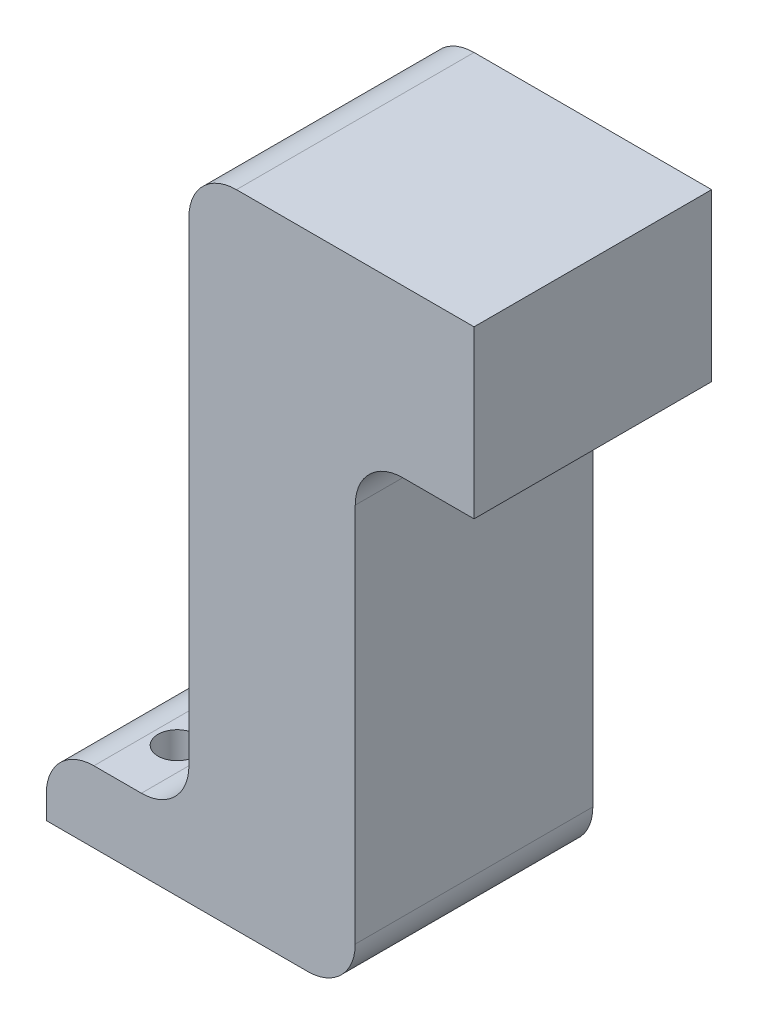
SolidWorks part; units mm, degrees
ref_plane "Front Plane" through (0, 0, 0) normal (0, 0, 1) x (1, 0, 0)
ref_plane "Top Plane" through (0, 0, 0) normal (0, 1, 0) x (1, 0, 0)
ref_plane "Right Plane" through (0, 0, 0) normal (1, 0, 0) x (0, 0, -1)
sketch "Sketch1" plane through (0, 0, 0) normal (0, 0, 1) x (1, 0, 0)
  line L0 (-1.4642, 0.25) -> (-1.4642, -4.75)
  line L5 (-1.4642, 0.25) -> (1.5358, 0.25)
  line L6 (-1.4642, 0.25) -> (-1.4642, 2)
  line L7 (-1.4642, 2) -> (1.5358, 2)
  line L8 (1.5358, 0.25) -> (1.5358, 2)
  line L9 (-1.4642, -4.75) -> (-2.9642, -4.75)
  line L10 (-1.4642, -4.75) -> (-1.4642, -4)
  line L11 (-1.4642, -4) -> (-2.9642, -4)
  line L12 (-2.9642, -4.75) -> (-2.9642, -4)
  line L13 (-1.4642, 0.25) -> (0.2858, 0.25)
  line L14 (-1.4642, -4.75) -> (0.2858, -4.75)
  line L15 (0.2858, 0.25) -> (0.2858, -4.75)
  dimension "D1" = 1.75
  dimension "D2" = 3
  dimension "D3" = 0
  dimension "D4" = 1.75
  dimension "D5" = 0.75
  dimension "D6" = 5
  dimension "D7" = 1.5
extrude "Boss-Extrude1" add sketch "Sketch1" along normal blind 1.875 and the other way blind 0.625 contours L5 L8 L7 L6 | L12 L9 L0 L11
fillet "Fillet1" radius 0.5 5 edges at (0.2858, 0.25, 0.625) (-1.4642, 2, 0.625) (-2.9642, -4, 0.625) (0.2858, -4.75, 0.625) (-1.4642, -4, 0.625)
hole_wizard "Ø0.4 (0.4) Diameter Hole1" positions "Sketch2" profile "Sketch3" hole size "Ø0.4" standard "DIN" end condition through all
sketch "Sketch2" plane through (0, -4, 0) normal (0, 1, 0) x (1, 0, 0)
  line L0 (-1.4642, 0) -> (-2.9642, 0) construction
  point P0 (-2.2142, 0)
  point P4 (-2.2142, -1.25)
  dimension "D1" = 1.25
sketch "Sketch3" plane through (-2.2142, -4, 0) normal (1, 0, 0) x (0, 0, 1)
  line L0 (0, 0) -> (0, 0.75)
  line L1 (0, 0.75) -> (0.2, 0.75)
  line L2 (0.2, 0.75) -> (0.2, 0)
  line L5 (0.2, 0) -> (0, 0)
  line L11 (0, -6.35) -> (0, 107.95) construction
  dimension "Thru Hole Dia." = 0.4
  dimension "Thru Hole Depth" = 0.75
